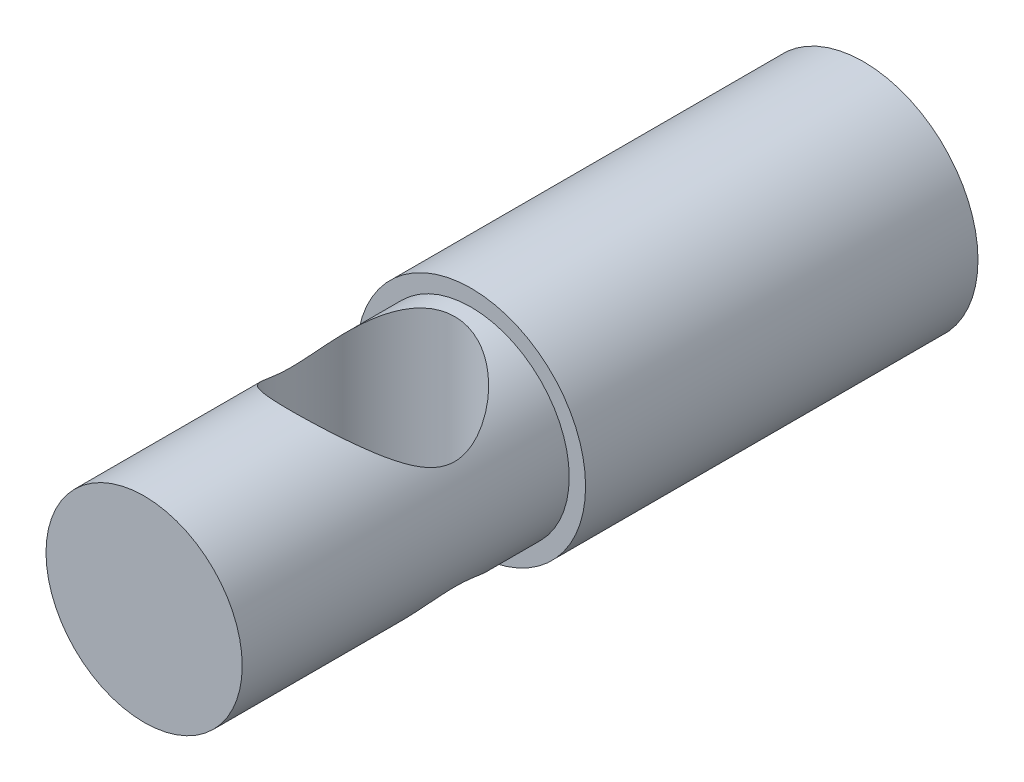
SolidWorks part; units mm, degrees
material "PLA"
ref_plane "Alzado" through (0, 0, 0) normal (0, 0, 1) x (1, 0, 0)
ref_plane "Planta" through (0, 0, 0) normal (0, 1, 0) x (1, 0, 0)
ref_plane "Vista lateral" through (0, 0, 0) normal (1, 0, 0) x (0, 0, -1)
sketch "Croquis1" plane through (0, 0, 0) normal (0, 0, 1) x (1, 0, 0)
  circle A0 centre (0, 0) radius 3.5
extrude "Saliente-Extruir1" add sketch "Croquis1" along normal blind 21
sketch "Croquis2" plane through (0, 0, 21) normal (0, 0, 1) x (1, 0, 0)
  circle A0 centre (0, 0) radius 3
  circle A1 centre (0, 0) radius 3.5
extrude "Cortar-Extruir1" cut sketch "Croquis2" against normal blind 10
sketch "Croquis3" plane through (0, 0, 0) normal (0, 1, 0) x (1, 0, 0)
  line L0 (0, -11) -> (0, -14) construction
  line L1 (-3, -11) -> (3, -11) construction
  circle A0 centre (0, -14) radius 2.5
extrude "Cortar-Extruir2" cut sketch "Croquis3" against normal blind 10
mirror "Simetría1" about plane through (0, 0, 0) normal (0, 1, 0) of "Cortar-Extruir2"
sketch "Croquis4" plane through (0, 0, 0) normal (0, 0, -1) x (-1, 0, 0)
  circle A0 centre (0, 0) radius 3.5
extrude "Saliente-Extruir2" add sketch "Croquis4" along normal blind 1
